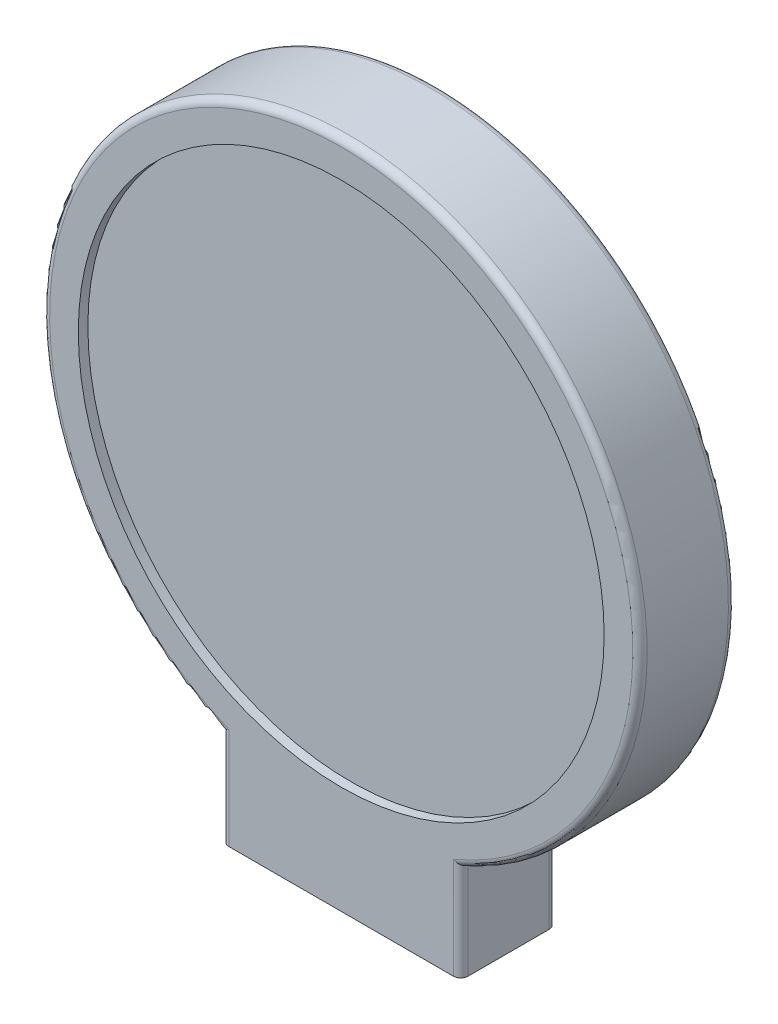
SolidWorks part; units mm, degrees
ref_plane "Front Plane" through (0, 0, 0) normal (0, 0, 1) x (1, 0, 0)
ref_plane "Top Plane" through (0, 0, 0) normal (0, 1, 0) x (1, 0, 0)
ref_plane "Right Plane" through (0, 0, 0) normal (1, 0, 0) x (0, 0, -1)
sketch "Sketch2" plane through (0, 0, 0) normal (0, 0, 1) x (1, 0, 0)
  line L0 (-50, 0) -> (50, 0)
  line L1 (-50, 0) -> (-50, 40.4356)
  line L3 (50, 40.4356) -> (50, 0)
  line L4 (0, 0) -> (0, 155) construction
  arc A0 (50, 40.4356) -> (-50, 40.4356) centre (0, 155) ccw
  circle A1 centre (0, 155) radius 110
  point P4 (0, 0)
  dimension "D2" = 220
  dimension "D1" = 100
  dimension "D3" = 155
extrude "Boss-Extrude1" add sketch "Sketch2" along normal blind 40
surface "Surface-Plane1"
sketch "Sketch5" plane through (0, 0, 0) normal (0, 0, -1) x (-1, 0, 0)
  circle A1 centre (0, 155) radius 110
  circle A2 centre (0, 155) radius 110
  dimension "D1" = 0
extrude "Boss-Extrude2" add sketch "Sketch5" against normal blind 36
fillet "Fillet1" radius 3 6 edges at (50, 20.2178, 0) (50, 20.2178, 40) (-50, 20.2178, 0) (-50, 20.2178, 40) (0, 280, 0) (0, 280, 40)
sketch "Sketch6" plane through (0, 0, 0) normal (0, -1, 0) x (1, 0, 0)
  line L0 (40, 30) -> (-40, 30)
  line L1 (-40, 30) -> (-40, 10)
  line L2 (-40, 10) -> (40, 10)
  line L3 (40, 10) -> (40, 30)
extrude "Cut-Extrude2" cut sketch "Sketch6" against normal blind 30
sketch "Sketch7" plane through (0, 30, 0) normal (0, -1, 0) x (1, 0, 0)
  line L0 (35, 25) -> (-35, 25)
  line L1 (-35, 25) -> (-35, 15)
  line L2 (-35, 15) -> (35, 15)
  line L3 (35, 15) -> (35, 25)
  line L4 (40, 10) -> (40, 30)
  line L5 (40, 30) -> (-40, 30)
  line L6 (-40, 30) -> (-40, 10)
  line L7 (-40, 10) -> (40, 10)
  line L8 (40, 10) -> (40, 30) construction
  line L9 (40, 30) -> (-40, 30) construction
  line L10 (-40, 30) -> (-40, 10) construction
  line L11 (-40, 10) -> (40, 10) construction
  dimension "D1" = 0
  dimension "D2" = 5
extrude "Boss-Extrude3" add sketch "Sketch7" along normal blind 30
sketch "Sketch8" plane through (0, 0, 25) normal (0, 0, 1) x (1, 0, 0)
  line L0 (35, 30) -> (-35, 30) construction
  line L1 (-35, 0) -> (-30, 0)
  line L2 (-35, 0) -> (-35, 30)
  line L3 (-35, 30) -> (-30, 30)
  line L4 (-30, 0) -> (-30, 30)
  line L5 (-25, 0) -> (-25, 30)
  line L6 (-25, 30) -> (-20, 30)
  line L7 (-20, 0) -> (-20, 30)
  line L8 (-25, 0) -> (-20, 0)
  line L9 (-15, 0) -> (-15, 30)
  line L10 (-15, 30) -> (-10, 30)
  line L11 (-10, 0) -> (-10, 30)
  line L12 (-15, 0) -> (-10, 0)
  line L13 (-5, 0) -> (-5, 30)
  line L14 (-5, 30) -> (0, 30)
  line L15 (0, 0) -> (0, 30)
  line L16 (-5, 0) -> (0, 0)
  line L17 (5, 0) -> (5, 30)
  line L18 (5, 30) -> (10, 30)
  line L19 (10, 0) -> (10, 30)
  line L20 (5, 0) -> (10, 0)
  line L21 (15, 0) -> (15, 30)
  line L22 (15, 30) -> (20, 30)
  line L23 (20, 0) -> (20, 30)
  line L24 (15, 0) -> (20, 0)
  line L25 (25, 0) -> (25, 30)
  line L26 (25, 30) -> (30, 30)
  line L27 (30, 0) -> (30, 30)
  line L28 (25, 0) -> (30, 0)
  dimension "D1" = 5
  dimension "D2" = 7
extrude "Boss-Extrude4" add sketch "Sketch8" along normal blind 3
sketch "Sketch10" plane through (0, 0, 0) normal (0, -1, 0) x (1, 0, 0)
  line L0 (0, 27.0143) -> (0, 15)
  line L2 (-35, 15) -> (35, 15) construction
  line L4 (0, 28) -> (0, 25) construction
  line L5 (0, 21.0072) -> (19.551, 21.0072) construction
ref_plane "Plane1" through (0, 0, 21.0072) normal (0, 0, 1) x (1, 0, 0)
mirror "Mirror2" about plane through (0, 0, 21.0072) normal (0, 0, 1) of "Boss-Extrude4"
